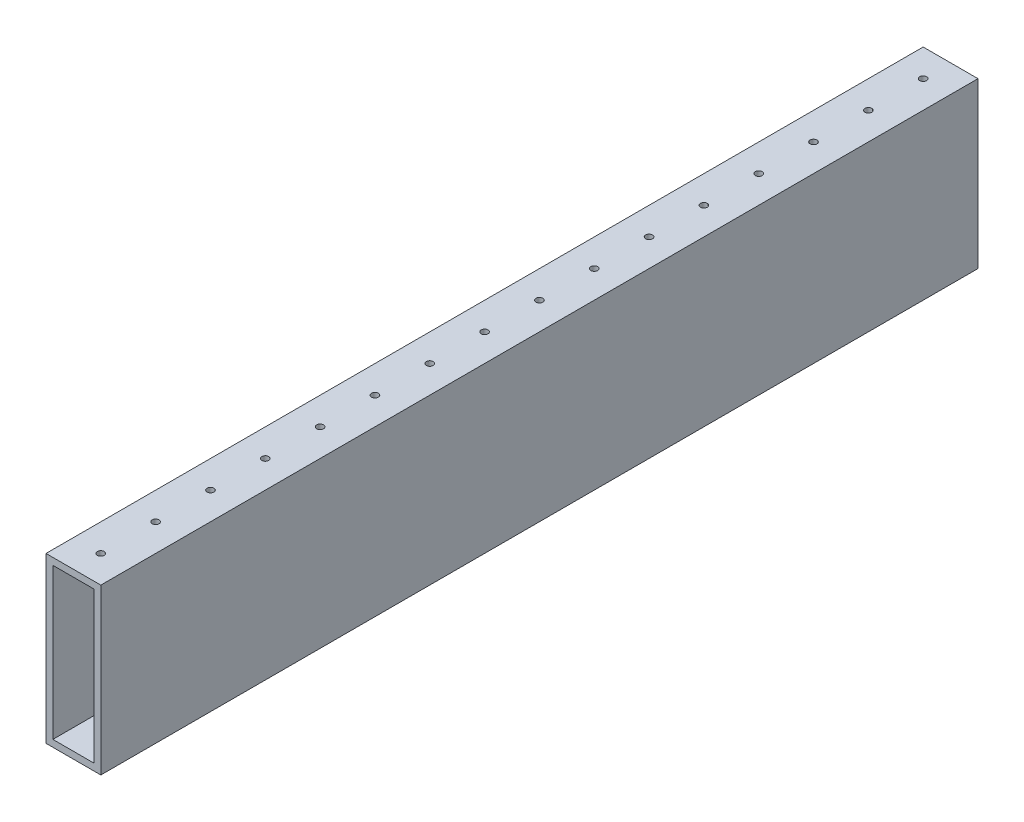
SolidWorks part; units mm, degrees
ref_plane "Front Plane" through (0, 0, 0) normal (0, 0, 1) x (1, 0, 0)
ref_plane "Top Plane" through (0, 0, 0) normal (0, 1, 0) x (1, 0, 0)
ref_plane "Right Plane" through (0, 0, 0) normal (1, 0, 0) x (0, 0, -1)
sketch "Sketch1" plane through (0, 0, 0) normal (0, 0, 1) x (1, 0, 0)
  line L1 (-12.7, -38.1) -> (12.7, -38.1)
  line L2 (-12.7, -38.1) -> (-12.7, 38.1)
  line L3 (-12.7, 38.1) -> (12.7, 38.1)
  line L4 (12.7, -38.1) -> (12.7, 38.1)
  line L5 (-12.7, -38.1) -> (12.7, 38.1) construction
  line L6 (-12.7, 38.1) -> (12.7, -38.1) construction
  point P0 (0, 0)
  dimension "D1" = 25.4
  dimension "D2" = 76.2
extrude "Boss-Extrude1" add sketch "Sketch1" along normal blind 406.4
shell "Shell1" thickness 3.175
sketch "Sketch2" plane through (0, 38.1, 0) normal (0, 1, 0) x (1, 0, 0)
  line L0 (12.7, 0) -> (-12.7, 0) construction
  circle A0 centre (0, -12.7) radius 1.5875
  dimension "D1" = 3.175
  dimension "D2" = 12.7
extrude "Cut-Extrude1" cut sketch "Sketch2" against normal blind 3.175
pattern_linear "LPattern1" count 16 spacing 25.4 along (0, 0, 1) of "Cut-Extrude1"
